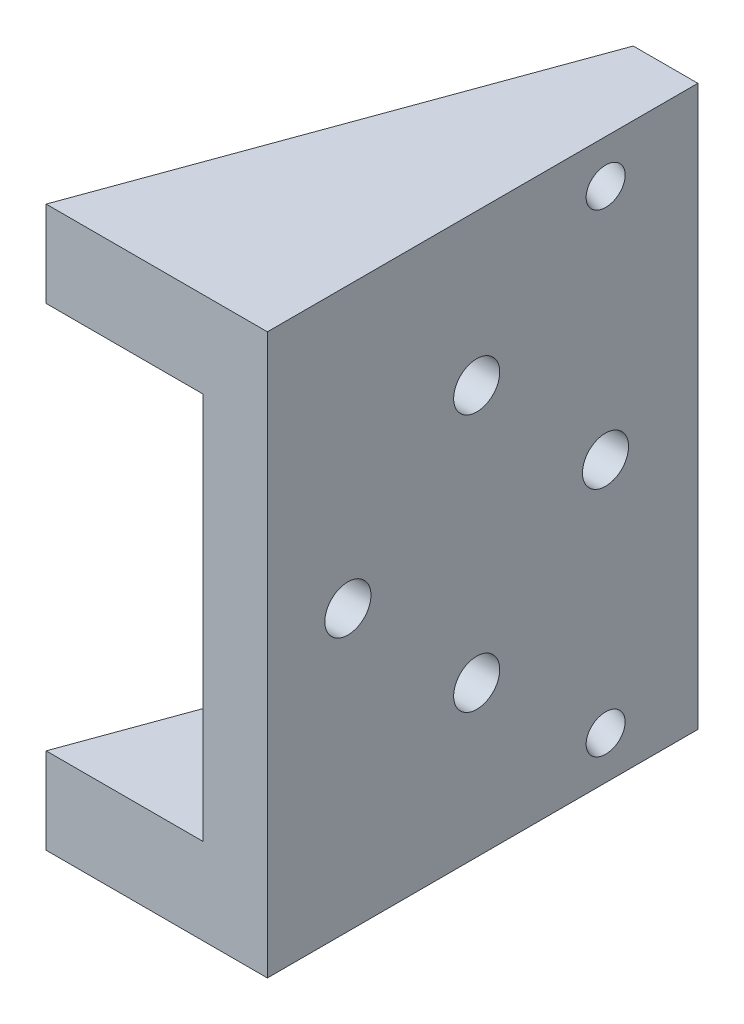
SolidWorks part; units mm, degrees
material "6061-T6 (SS)"
ref_plane "Front Plane" through (0, 0, 0) normal (0, 0, 1) x (1, 0, 0)
ref_plane "Top Plane" through (0, 0, 0) normal (0, 1, 0) x (1, 0, 0)
ref_plane "Right Plane" through (0, 0, 0) normal (1, 0, 0) x (0, 0, -1)
sketch "Sketch1" plane through (0, 0, 0) normal (0, 1, 0) x (1, 0, 0)
  line L0 (0, 0) -> (-11.5561, -31.75)
  line L1 (0, 0) -> (4.7625, 0)
  line L2 (0, -31.75) -> (0, 0) construction
  line L3 (4.7625, 0) -> (4.7625, -31.75)
  line L4 (4.7625, -31.75) -> (-11.5561, -31.75)
  dimension "D1" = 20
  dimension "D2" = 4.7625
  dimension "D4" = 31.75
extrude "Boss-Extrude1" add sketch "Sketch1" along normal mid plane 41.275
hole_wizard "M3 Clearance Hole1" positions "Sketch5" profile "Sketch6" hole size "M3" standard "ANSI Metric" end condition through all
sketch "Sketch5" plane through (4.7625, 0, 0) normal (1, 0, 0) x (0, 0, -1)
  line L0 (-31.75, 0) -> (0, 0) construction
  line L1 (-31.75, 20.6375) -> (-31.75, -20.6375) construction
  line L5 (-16.3125, 9.5) -> (-6.8125, 0) construction
  line L6 (-6.8125, 0) -> (-16.3125, -9.5) construction
  line L7 (-16.3125, -9.5) -> (-25.8125, 0) construction
  line L8 (-25.8125, 0) -> (-16.3125, 9.5) construction
  line L9 (0, 20.6375) -> (0, -20.6375) construction
  circle A0 centre (-16.3125, 0) radius 13.85 construction
  point P14 (-16.3125, 9.5)
  point P15 (-6.8125, 0)
  point P17 (-16.3125, -9.5)
  point P19 (-25.8125, 0)
  dimension "D1" = 27.7
  dimension "D4" = 1.5875
  dimension "D2" = 4.35
  dimension "D3" = 19
sketch "Sketch6" plane through (4.7625, 9.5, 16.3125) normal (0, 1, 0) x (0, 0, -1)
  line L0 (0, 0) -> (0, 16.3186)
  line L1 (0, 16.3186) -> (1.7, 16.3186)
  line L2 (1.7, 16.3186) -> (1.7, 0)
  line L5 (1.7, 0) -> (0, 0)
  line L11 (0, -6.35) -> (0, 107.95) construction
  dimension "Thru Hole Dia." = 3.4
  dimension "Thru Hole Depth" = 16.3186
sketch "Sketch15" plane through (0, 0, 0) normal (0, 1, 0) x (1, 0, 0)
  line L0 (-11.5561, -31.75) -> (0, 0)
  line L1 (0, 0) -> (-11.5561, -31.75) construction
  line L3 (-11.5561, -31.75) -> (0, -31.75)
  line L4 (0, -31.75) -> (0, 0)
  line L5 (0, -31.75) -> (0, 0)
  line L7 (-11.5561, -31.75) -> (4.7625, -31.75) construction
  dimension "D1" = 4.7625
extrude "Cut-Extrude1" cut sketch "Sketch15" along direction (0, -1, 0) on the side of the normal offset from surface 6.35 and the other way offset from surface (14.2875 mm away) 6.35
hole_wizard "#6-32 Tapped Hole1" positions "Sketch18" profile "Sketch17" tap size "#6-32" standard "ANSI Inch"
sketch "Sketch18" plane through (0, 0, 0) normal (-0.9397, 0, -0.342) x (-0.342, 0, 0.9397)
  line L0 (0, 17.4625) -> (33.7876, 17.4625) construction
  line L1 (0, 20.6375) -> (0, 14.2875) construction
  line L2 (33.7876, 20.6375) -> (33.7876, 14.2875) construction
  line L3 (0, 0) -> (29.8352, 0) construction
  line L4 (29.8352, 14.2875) -> (29.8352, -14.2875) construction
  point P11 (4.7625, 17.4625)
  point P13 (26.9875, 17.4625)
  point P23 (26.9875, -17.4625)
  point P24 (4.7625, -17.4625)
  dimension "D1" = 22.225
  dimension "D2" = 4.7625
sketch "Sketch17" plane through (-1.6289, 17.4625, 4.4753) normal (0, 1, 0) x (-0.342, 0, 0.9397)
  line L0 (0, 0) -> (0, 9.1947)
  line L1 (0, 9.1947) -> (1.3525, 8.382)
  line L2 (1.3525, 8.382) -> (1.3525, 0)
  line L5 (1.3525, 0) -> (0, 0)
  line L10 (0, 9.1947) -> (-1.3526, 8.382) construction
  line L11 (0, -6.35) -> (0, 107.95) construction
  dimension "Tap Drill Dia." = 2.7051
  dimension "Tap Drill Depth" = 8.382
  dimension "Drill Angle" = 118
